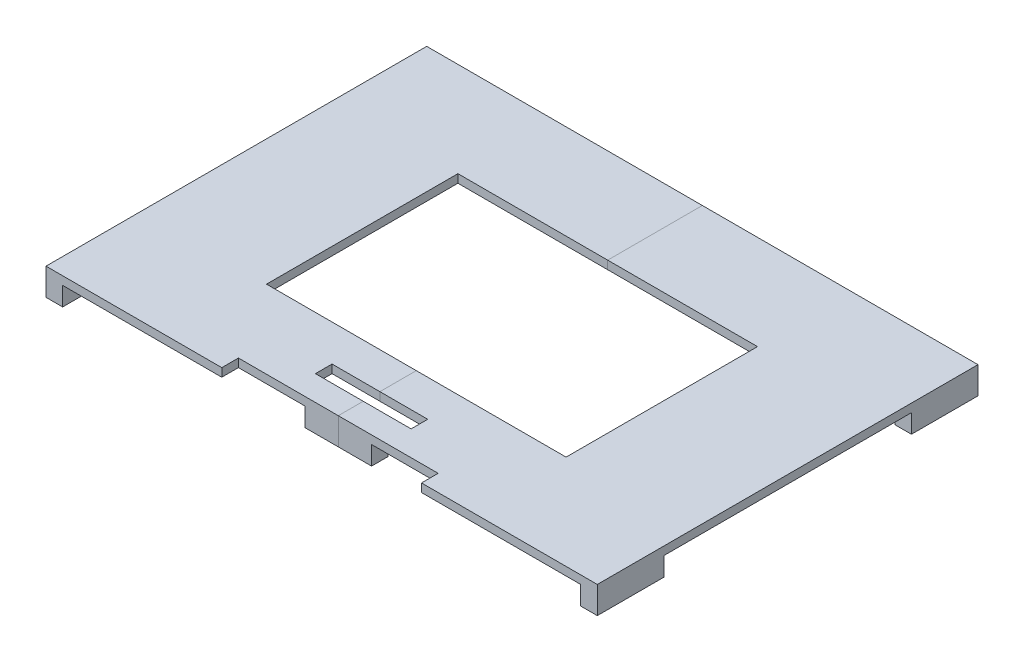
SolidWorks part; units mm, degrees
ref_plane "Front Plane" through (0, 0, 0) normal (0, 0, 1) x (1, 0, 0)
ref_plane "Top Plane" through (0, 0, 0) normal (0, 1, 0) x (1, 0, 0)
ref_plane "Right Plane" through (0, 0, 0) normal (1, 0, 0) x (0, 0, -1)
sketch "Sketch1" plane through (0, 0, 0) normal (0, 1, 0) x (1, 0, 0)
  line L1 (-210.3438, -145.2563) -> (210.3438, -145.2563)
  line L2 (-210.3438, -145.2563) -> (-210.3438, 145.2562)
  line L3 (-210.3438, 145.2562) -> (210.3438, 145.2562)
  line L4 (210.3438, -145.2563) -> (210.3438, 145.2562)
  line L5 (-210.3438, -145.2563) -> (210.3438, 145.2562) construction
  line L6 (-210.3438, 145.2562) -> (210.3438, -145.2563) construction
  point P0 (0, 0)
  dimension "D1" = 420.6875
  dimension "D2" = 290.5125
extrude "Boss-Extrude1" add sketch "Sketch1" along normal blind 6.35
sketch "Sketch2" plane through (0, 6.35, 0) normal (0, 1, 0) x (1, 0, 0)
  line L0 (-210.3438, -145.2563) -> (210.3438, -145.2563) construction
  line L1 (-114.3, -73.025) -> (114.3, -73.025)
  line L2 (-114.3, -73.025) -> (-114.3, 73.025)
  line L3 (-114.3, 73.025) -> (114.3, 73.025)
  line L4 (114.3, -73.025) -> (114.3, 73.025)
  line L5 (-114.3, -73.025) -> (114.3, 73.025) construction
  line L6 (-114.3, 73.025) -> (114.3, -73.025) construction
  line L7 (-36.5125, -113.5063) -> (36.5125, -113.5063)
  line L8 (-36.5125, -113.5063) -> (-36.5125, -100.8063)
  line L9 (-36.5125, -100.8063) -> (36.5125, -100.8063)
  line L10 (36.5125, -113.5063) -> (36.5125, -100.8063)
  line L11 (-36.5125, -113.5063) -> (36.5125, -100.8063) construction
  line L12 (-36.5125, -100.8063) -> (36.5125, -113.5063) construction
  line L13 (-76.2, -132.5563) -> (76.2, -132.5563)
  line L14 (-76.2, -132.5563) -> (-76.2, -145.2563)
  line L15 (-76.2, -145.2563) -> (76.2, -145.2563)
  line L16 (76.2, -132.5563) -> (76.2, -145.2563)
  line L17 (-76.2, -132.5563) -> (76.2, -145.2563) construction
  line L18 (-76.2, -145.2563) -> (76.2, -132.5563) construction
  point P0 (0, 0)
  point P6 (0, -107.1563)
  point P12 (0, -138.9062)
  dimension "D1" = 228.6
  dimension "D2" = 146.05
  dimension "D3" = 73.025
  dimension "D4" = 12.7
  dimension "D5" = 38.1
  dimension "D6" = 6.35
  dimension "D7" = 152.4
extrude "Cut-Extrude1" cut sketch "Sketch2" against normal through all
sketch "Sketch4" plane through (0, 0, 0) normal (0, -1, 0) x (1, 0, 0)
  line L0 (-210.3438, -145.2562) -> (-210.3438, 145.2563) construction
  line L1 (-197.6438, 94.4563) -> (-210.3438, 94.4563)
  line L2 (-197.6438, 94.4563) -> (-197.6438, 145.2563)
  line L3 (-197.6438, 145.2563) -> (-210.3438, 145.2563)
  line L4 (-210.3438, 94.4563) -> (-210.3438, 145.2563)
  line L5 (-197.6438, 94.4563) -> (-210.3438, 145.2563) construction
  line L6 (-197.6438, 145.2563) -> (-210.3438, 94.4563) construction
  line L7 (197.6438, 94.4563) -> (210.3438, 94.4563)
  line L8 (197.6438, 94.4563) -> (197.6438, 145.2563)
  line L9 (197.6438, 145.2563) -> (210.3438, 145.2563)
  line L10 (210.3438, 94.4563) -> (210.3438, 145.2563)
  line L11 (197.6438, 94.4563) -> (210.3438, 145.2563) construction
  line L12 (197.6438, 145.2563) -> (210.3438, 94.4563) construction
  line L13 (-197.6438, -94.4562) -> (-210.3438, -94.4562)
  line L14 (-197.6438, -94.4562) -> (-197.6438, -145.2562)
  line L15 (-197.6438, -145.2562) -> (-210.3438, -145.2562)
  line L16 (-210.3438, -94.4562) -> (-210.3438, -145.2562)
  line L17 (-197.6438, -94.4562) -> (-210.3438, -145.2562) construction
  line L18 (-197.6438, -145.2562) -> (-210.3438, -94.4562) construction
  line L19 (210.3438, 145.2563) -> (210.3438, -145.2562) construction
  line L20 (197.6438, -94.4562) -> (210.3438, -94.4562)
  line L21 (197.6438, -94.4562) -> (197.6438, -145.2562)
  line L22 (197.6438, -145.2562) -> (210.3438, -145.2562)
  line L23 (210.3438, -94.4562) -> (210.3438, -145.2562)
  line L24 (197.6438, -94.4562) -> (210.3438, -145.2562) construction
  line L25 (197.6438, -145.2562) -> (210.3438, -94.4562) construction
  line L31 (76.2, 132.5563) -> (-76.2, 132.5563) construction
  line L32 (25.4, 119.8563) -> (-25.4, 119.8563)
  line L33 (25.4, 119.8563) -> (25.4, 132.5563)
  line L34 (25.4, 132.5563) -> (-25.4, 132.5563)
  line L35 (-25.4, 119.8563) -> (-25.4, 132.5563)
  line L36 (25.4, 119.8563) -> (-25.4, 132.5563) construction
  line L37 (25.4, 132.5563) -> (-25.4, 119.8563) construction
  line L38 (210.3438, -145.2562) -> (-210.3438, -145.2562) construction
  line L39 (25.4, -132.5562) -> (-25.4, -132.5562)
  line L40 (25.4, -132.5562) -> (25.4, -145.2562)
  line L41 (25.4, -145.2562) -> (-25.4, -145.2562)
  line L42 (-25.4, -132.5562) -> (-25.4, -145.2562)
  line L43 (25.4, -132.5562) -> (-25.4, -145.2562) construction
  line L44 (25.4, -145.2562) -> (-25.4, -132.5562) construction
  point P0 (-203.9938, 119.8563)
  point P6 (203.9938, 119.8563)
  point P12 (-203.9938, -119.8562)
  point P19 (203.9938, -119.8562)
  point P26 (0, -138.9062)
  point P32 (0, 126.2063)
  point P41 (0, 0)
  dimension "D1" = 12.7
  dimension "D2" = 50.8
  dimension "D3" = 12.7
  dimension "D4" = 50.8
  dimension "D5" = 12.7
  dimension "D6" = 50.8
  dimension "D7" = 12.7
  dimension "D8" = 50.8
  dimension "D9" = 50.8
  dimension "D10" = 12.7
  dimension "D11" = 50.8
  dimension "D12" = 12.7
extrude "Boss-Extrude2" add sketch "Sketch4" along normal blind 14.2875
split "Split1" trim tools "Right Plane" bodies to split 103 resulting bodies 104 105
